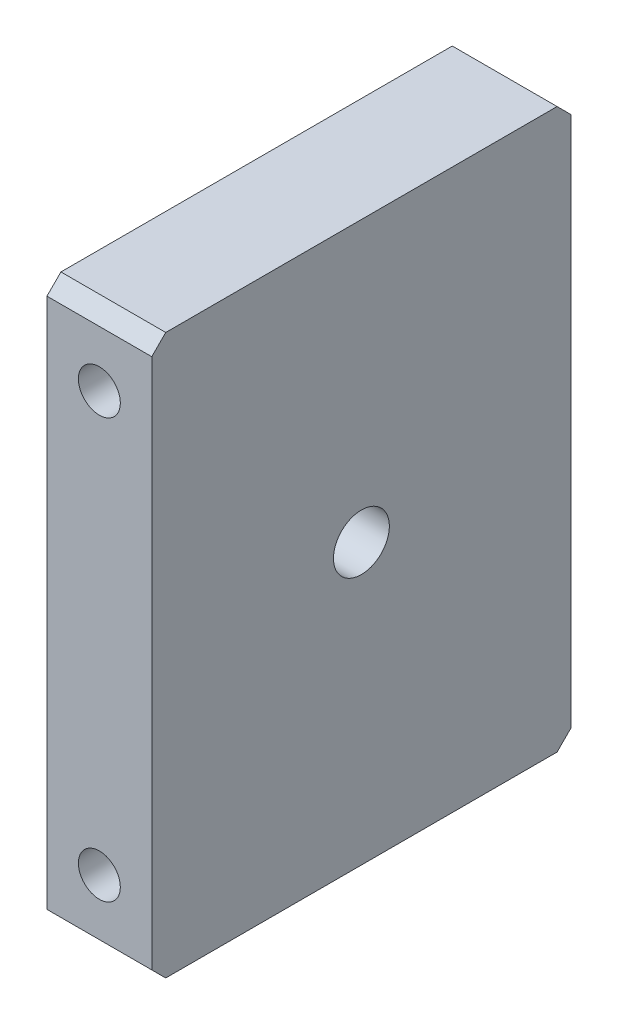
SolidWorks part; units mm, degrees
ref_plane "Front Plane" through (0, 0, 0) normal (0, 0, 1) x (1, 0, 0)
ref_plane "Top Plane" through (0, 0, 0) normal (0, 1, 0) x (1, 0, 0)
ref_plane "Right Plane" through (0, 0, 0) normal (1, 0, 0) x (0, 0, -1)
sketch "Sketch1" plane through (0, 0, 0) normal (1, 0, 0) x (0, 0, -1)
  line L0 (0, 101.6) -> (0, 0)
  line L1 (76.2, 101.6) -> (76.2, 0)
  line L5 (0, 101.6) -> (76.2, 101.6)
  line L11 (76.2, 0) -> (0, 0)
  dimension "D1" = 76.2
  dimension "D4" = 101.6
extrude "Boss-Extrude1" add sketch "Sketch1" along normal blind 19.05
sketch "Sketch3" plane through (0, 0, 0) normal (0, 0, 1) x (1, 0, 0)
  line L1 (19.05, 0) -> (0, 0) construction
  circle A0 centre (9.525, 12.7) radius 3.81
  dimension "D1" = 12.7
extrude "Cut-Extrude2" cut sketch "Sketch3" against normal through all
sketch "Sketch6" plane through (0, 0, 0) normal (0, 0, 1) x (1, 0, 0)
  line L0 (19.05, 101.6) -> (0, 101.6) construction
  circle A0 centre (9.525, 88.9) radius 3.81
  dimension "D1" = 12.7
extrude "Cut-Extrude5" cut sketch "Sketch6" against normal through all
sketch "Sketch5" plane through (19.05, 0, 0) normal (1, 0, 0) x (0, 0, -1)
  line L0 (38.1, 101.6) -> (38.1, 0) construction
  line L1 (76.2, 101.6) -> (0, 101.6) construction
  line L2 (0, 0) -> (76.2, 0) construction
  circle A0 centre (38.1, 50.8) radius 5.08
extrude "Cut-Extrude4" cut sketch "Sketch5" against normal through all
chamfer "Chamfer1" distance 2.54 angle 45 4 edges at (9.525, 0, -76.2) (9.525, 0, 0) (9.525, 101.6, -76.2) (9.525, 101.6, 0)
